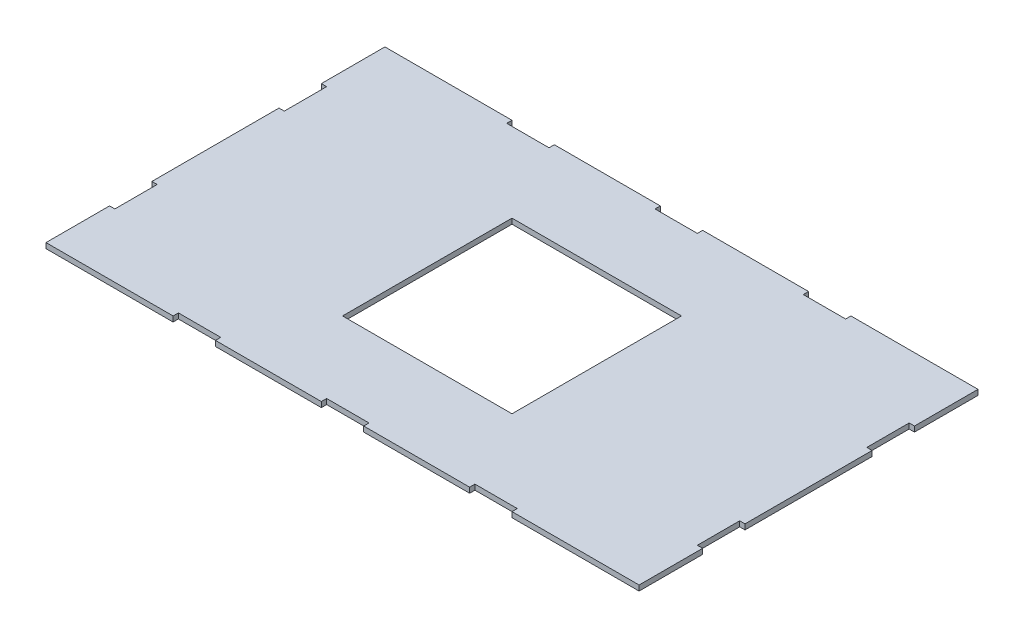
SolidWorks part; units mm, degrees
ref_plane "Front Plane" through (0, 0, 0) normal (0, 0, 1) x (1, 0, 0)
ref_plane "Top Plane" through (0, 0, 0) normal (0, 1, 0) x (1, 0, 0)
ref_plane "Right Plane" through (0, 0, 0) normal (1, 0, 0) x (0, 0, -1)
sketch "Sketch1" plane through (0, 0, 0) normal (0, 1, 0) x (1, 0, 0)
  line L1 (0, 0) -> (355.6, 0)
  line L2 (0, 0) -> (0, 203.2)
  line L3 (0, 203.2) -> (355.6, 203.2)
  line L4 (355.6, 0) -> (355.6, 203.2)
  dimension "D1" = 203.2
  dimension "D2" = 355.6
extrude "Boss-Extrude1" add sketch "Sketch1" along normal blind 3.175
sketch "Sketch2" plane through (0, 3.175, 0) normal (0, 1, 0) x (1, 0, 0)
  line L0 (0, 203.2) -> (0, 0) construction
  line L1 (127, 50.8) -> (228.6, 50.8)
  line L2 (127, 50.8) -> (127, 152.4)
  line L3 (127, 152.4) -> (228.6, 152.4)
  line L4 (228.6, 50.8) -> (228.6, 152.4)
  line L5 (355.6, 203.2) -> (0, 203.2) construction
  point P6 (0, 101.6)
  point P7 (127, 101.6)
  point P10 (177.8, 203.2)
  point P11 (177.8, 152.4)
  dimension "D1" = 101.6
  dimension "D2" = 101.6
extrude "Cut-Extrude1" cut sketch "Sketch2" against normal through all contours L2 L3 L4 L1
sketch "Sketch3" [suppressed] plane through (0, 3.175, 0) normal (0, 1, 0) x (1, 0, 0)
  line L0 (0, 0) -> (355.6, 0) construction
  line L1 (12.7, 0) -> (35.179, 0)
  line L2 (12.7, 0) -> (12.7, 76.2)
  line L3 (12.7, 76.2) -> (35.179, 76.2)
  line L4 (35.179, 0) -> (35.179, 76.2)
  line L5 (0, 203.2) -> (0, 0) construction
  dimension "D1" = 76.2
  dimension "D2" = 22.479
  dimension "D3" = 12.7
extrude "Cut-Extrude2" [suppressed] cut sketch "Sketch3" against normal through all
sketch "Sketch4" plane through (0, 3.175, 0) normal (0, 1, 0) x (1, 0, 0)
  line L0 (0, 0) -> (355.6, 0) construction
  line L1 (76.2, 0) -> (101.6, 0)
  line L2 (76.2, 0) -> (76.2, 3.175)
  line L3 (76.2, 3.175) -> (101.6, 3.175)
  line L4 (101.6, 0) -> (101.6, 3.175)
  line L5 (0, 203.2) -> (0, 0) construction
  line L6 (165.1, 0) -> (190.5, 0)
  line L7 (165.1, 0) -> (165.1, 3.175)
  line L8 (165.1, 3.175) -> (190.5, 3.175)
  line L9 (190.5, 0) -> (190.5, 3.175)
  line L10 (254, 0) -> (279.4, 0)
  line L11 (254, 0) -> (254, 3.175)
  line L12 (254, 3.175) -> (279.4, 3.175)
  line L13 (279.4, 0) -> (279.4, 3.175)
  line L14 (355.6, 0) -> (355.6, 203.2) construction
  line L15 (0, 101.6) -> (355.6, 101.6) construction
  line L16 (254, 200.025) -> (279.4, 200.025)
  line L17 (279.4, 203.2) -> (279.4, 200.025)
  line L18 (254, 203.2) -> (279.4, 203.2)
  line L19 (254, 203.2) -> (254, 200.025)
  line L20 (165.1, 200.025) -> (190.5, 200.025)
  line L21 (190.5, 203.2) -> (190.5, 200.025)
  line L22 (165.1, 203.2) -> (190.5, 203.2)
  line L23 (165.1, 203.2) -> (165.1, 200.025)
  line L24 (76.2, 200.025) -> (101.6, 200.025)
  line L25 (101.6, 203.2) -> (101.6, 200.025)
  line L26 (76.2, 203.2) -> (101.6, 203.2)
  line L27 (76.2, 203.2) -> (76.2, 200.025)
  line L28 (355.6, 203.2) -> (0, 203.2) construction
  line L29 (0, 165.1) -> (3.175, 165.1)
  line L30 (0, 165.1) -> (0, 139.7)
  line L31 (0, 139.7) -> (3.175, 139.7)
  line L32 (3.175, 165.1) -> (3.175, 139.7)
  line L33 (0, 63.5) -> (3.175, 63.5)
  line L34 (0, 63.5) -> (0, 38.1)
  line L35 (0, 38.1) -> (3.175, 38.1)
  line L36 (3.175, 63.5) -> (3.175, 38.1)
  line L37 (177.8, 203.2) -> (177.8, 0) construction
  line L38 (355.6, 38.1) -> (352.425, 38.1)
  line L39 (352.425, 63.5) -> (352.425, 38.1)
  line L40 (355.6, 63.5) -> (352.425, 63.5)
  line L41 (355.6, 63.5) -> (355.6, 38.1)
  line L42 (355.6, 139.7) -> (352.425, 139.7)
  line L43 (352.425, 165.1) -> (352.425, 139.7)
  line L44 (355.6, 165.1) -> (352.425, 165.1)
  line L45 (355.6, 165.1) -> (355.6, 139.7)
  point P18 (177.8, 0)
  point P19 (177.8, 3.175)
  dimension "D1" = 3.175
  dimension "D2" = 25.4
  dimension "D3" = 25.4
  dimension "D4" = 25.4
  dimension "D5" = 3.175
  dimension "D6" = 3.175
  dimension "D7" = 76.2
  dimension "D8" = 76.2
  dimension "D9" = 3.175
  dimension "D10" = 3.175
  dimension "D11" = 25.4
  dimension "D12" = 25.4
  dimension "D13" = 38.1
  dimension "D14" = 38.1
extrude "Cut-Extrude3" cut sketch "Sketch4" against normal through all
sketch "Sketch5" [suppressed] plane through (0, 0, 0) normal (0, 0, 1) x (1, 0, 0)
  line L0 (35.179, 3.175) -> (355.6, 3.175) construction
  line L1 (76.2, 3.175) -> (101.6, 3.175)
  line L2 (76.2, 3.175) -> (76.2, 0)
  line L3 (76.2, 0) -> (101.6, 0)
  line L4 (101.6, 3.175) -> (101.6, 0)
  line L5 (35.179, 0) -> (355.6, 0) construction
  line L6 (0, 3.175) -> (0, 0) construction
  line L7 (254, 0) -> (279.4, 0)
  line L8 (254, 0) -> (254, 3.175)
  line L9 (254, 3.175) -> (279.4, 3.175)
  line L10 (279.4, 0) -> (279.4, 3.175)
  line L11 (355.6, 3.175) -> (355.6, 0) construction
  line L12 (355.6, 3.175) -> (0, 3.175) construction
  line L17 (165.1, 0) -> (190.5, 0)
  line L18 (165.1, 0) -> (165.1, 3.175)
  line L19 (165.1, 3.175) -> (190.5, 3.175)
  line L20 (190.5, 0) -> (190.5, 3.175)
  point P23 (177.8, 3.175)
  point P24 (177.8, 3.175)
  dimension "D1" = 76.2
  dimension "D2" = 25.4
  dimension "D3" = 76.2
  dimension "D4" = 25.4
  dimension "D5" = 25.4
extrude "Boss-Extrude2" [suppressed] add sketch "Sketch5" along normal blind 3.175
